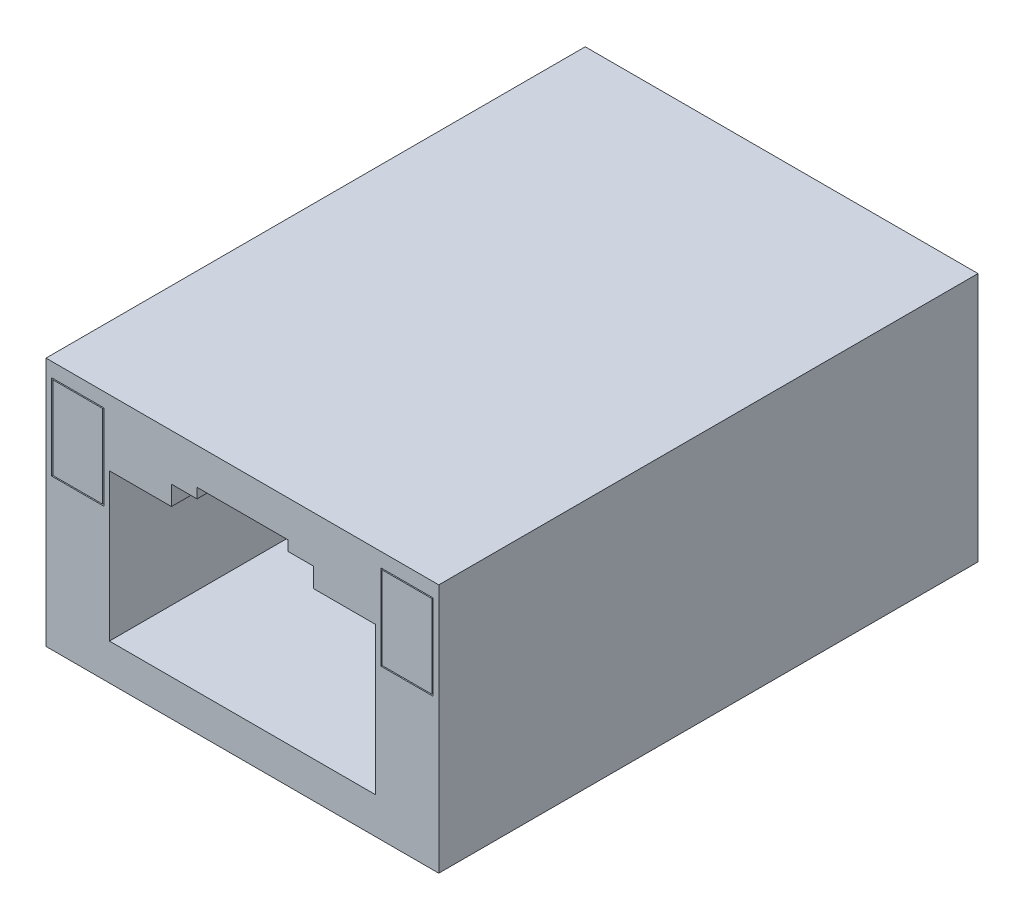
SolidWorks part; units mm, degrees
ref_plane "Front Plane" through (0, 0, 0) normal (0, 0, 1) x (1, 0, 0)
ref_plane "Top Plane" through (0, 0, 0) normal (0, 1, 0) x (1, 0, 0)
ref_plane "Right Plane" through (0, 0, 0) normal (1, 0, 0) x (0, 0, -1)
sketch "Sketch1" plane through (0, 0, 0) normal (0, 0, 1) x (1, 0, 0)
  line L1 (0, 0) -> (17.5768, 0)
  line L2 (0, 0) -> (0, 11.176)
  line L3 (0, 11.176) -> (17.5768, 11.176)
  line L4 (17.5768, 0) -> (17.5768, 11.176)
  dimension "D1" = 17.5768
  dimension "D2" = 11.176
extrude "Boss-Extrude1" add sketch "Sketch1" against normal blind 24.13
sketch "Sketch2" plane through (0, 0, 0) normal (0, 0, 1) x (1, 0, 0)
  line L0 (2.8384, 1.628) -> (14.7384, 1.628)
  line L1 (14.7384, 1.628) -> (14.7384, 8.228)
  line L2 (14.7384, 8.228) -> (11.9634, 8.228)
  line L3 (11.9634, 8.228) -> (11.9634, 9.098)
  line L4 (11.9634, 9.098) -> (10.8184, 9.098)
  line L5 (5.6134, 9.098) -> (5.6134, 8.228)
  line L6 (5.6134, 8.228) -> (2.8384, 8.228)
  line L7 (2.8384, 8.228) -> (2.8384, 1.628)
  line L8 (8.7884, 1.628) -> (8.7884, 0) construction
  line L9 (0, 0) -> (17.5768, 0) construction
  line L10 (6.7584, 9.098) -> (6.7584, 9.548)
  line L11 (6.7584, 9.548) -> (10.8184, 9.548)
  line L12 (10.8184, 9.548) -> (10.8184, 9.098)
  line L13 (6.7584, 9.098) -> (5.6134, 9.098)
  line L14 (8.7884, 9.548) -> (8.7884, 11.176) construction
  line L15 (17.5768, 11.176) -> (0, 11.176) construction
  dimension "D1" = 11.9
  dimension "D2" = 6.35
  dimension "D3" = 4.06
  dimension "D4" = 6.6
  dimension "D5" = 7.47
  dimension "D6" = 7.92
extrude "Cut-Extrude1" cut sketch "Sketch2" against normal blind 22.55
sketch "Sketch3" plane through (0, 0, 0) normal (0, 0, 1) x (1, 0, 0)
  line L0 (0, 11.176) -> (0, 0) construction
  line L1 (0.254, 10.541) -> (2.5844, 10.541)
  line L2 (0.254, 10.541) -> (0.254, 6.731)
  line L3 (0.254, 6.731) -> (2.5844, 6.731)
  line L4 (2.5844, 10.541) -> (2.5844, 6.731)
  line L5 (14.9924, 10.541) -> (17.3228, 10.541)
  line L6 (14.9924, 10.541) -> (14.9924, 6.731)
  line L7 (14.9924, 6.731) -> (17.3228, 6.731)
  line L8 (17.3228, 10.541) -> (17.3228, 6.731)
  line L9 (17.5768, 0) -> (17.5768, 11.176) construction
  line L10 (17.5768, 11.176) -> (0, 11.176) construction
  line L11 (2.8384, 8.228) -> (2.8384, 1.628) construction
  line L13 (0.3048, 10.4902) -> (2.5336, 10.4902)
  line L14 (0.3048, 10.4902) -> (0.3048, 6.7818)
  line L15 (0.3048, 6.7818) -> (2.5336, 6.7818)
  line L16 (2.5336, 10.4902) -> (2.5336, 6.7818)
  line L17 (15.0432, 10.4902) -> (17.272, 10.4902)
  line L18 (15.0432, 10.4902) -> (15.0432, 6.7818)
  line L19 (15.0432, 6.7818) -> (17.272, 6.7818)
  line L20 (17.272, 10.4902) -> (17.272, 6.7818)
  dimension "D1" = 0.254
  dimension "D2" = 0.254
  dimension "D3" = 0.635
  dimension "D4" = 0.254
  dimension "D5" = 3.81
  dimension "D6" = 0.0508
  dimension "D7" = 0.0508
  dimension "D8" = 0.0508
  dimension "D9" = 0.0508
  dimension "D10" = 0.0508
extrude "Cut-Extrude2" cut sketch "Sketch3" against normal blind 0.254
sketch "Sketch4" plane through (0, 0, 0) normal (0, -1, 0) x (1, 0, 0)
  line L0 (17.5768, -24.13) -> (17.5768, 0) construction
  line L1 (-0.1016, -24.13) -> (17.6784, -24.13)
  line L2 (-0.1016, -24.13) -> (-0.1016, 0)
  line L3 (-0.1016, 0) -> (17.6784, 0)
  line L4 (17.6784, -24.13) -> (17.6784, 0)
  line L5 (-0.1016, -24.13) -> (17.6784, 0) construction
  line L6 (-0.1016, 0) -> (17.6784, -24.13) construction
  line L7 (0, -24.13) -> (17.5768, -24.13) construction
  point P0 (8.7884, -12.065)
  point P7 (17.5768, -12.065)
  point P10 (8.7884, -24.13)
  dimension "D1" = 17.78
  dimension "D2" = 24.13
